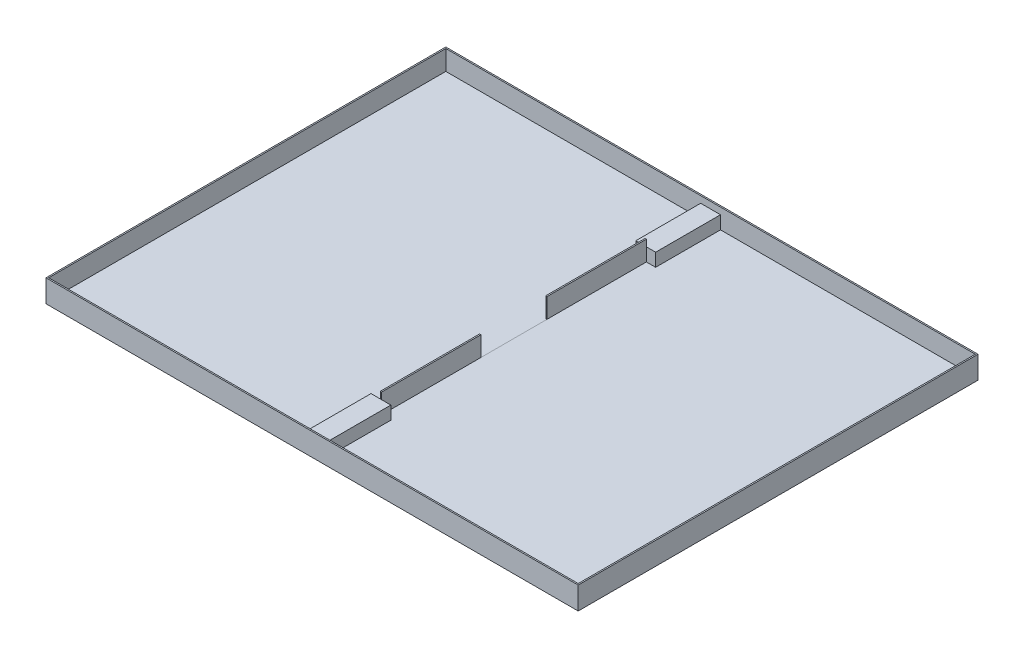
SolidWorks part; units mm, degrees
material "Balsa"
ref_plane "Plano frontal" through (0, 0, 0) normal (0, 0, 1) x (1, 0, 0)
ref_plane "Plano superior" through (0, 0, 0) normal (0, 1, 0) x (1, 0, 0)
ref_plane "Plano direito" through (0, 0, 0) normal (1, 0, 0) x (0, 0, -1)
sketch "Esboço1" plane through (0, 0, 0) normal (0, 0, 1) x (1, 0, 0)
  line L0 (3179.7534, -132.1233) -> (-840.2466, -132.1233)
  line L1 (-840.2466, -132.1233) -> (-840.2466, -152.1233)
  line L4 (-840.2466, -152.1233) -> (3179.7534, -152.1233)
  line L5 (3179.7534, -152.1233) -> (3179.7534, -132.1233)
  dimension "D1" = 4020
  dimension "D3" = 20
extrude "Ressalto-extrusão1" add sketch "Esboço1" along normal blind 3020
sketch "Esboço2" plane through (0, -132.1233, 0) normal (0, 1, 0) x (1, 0, 0)
  line L0 (-830.2466, -10) -> (-830.2466, -3010)
  line L1 (-840.2466, 0) -> (3179.7534, 0)
  line L2 (-840.2466, 0) -> (-840.2466, -3020)
  line L3 (-840.2466, -3020) -> (3179.7534, -3020)
  line L4 (3179.7534, 0) -> (3179.7534, -3020)
  line L5 (-830.2466, -3010) -> (3169.7534, -3010)
  line L6 (3169.7534, -10) -> (3169.7534, -3010)
  line L7 (-830.2466, -10) -> (3169.7534, -10)
  line L8 (1169.7534, -500) -> (1169.7534, -1250) construction
  line L9 (1164.7534, -500) -> (1164.7534, -1250)
  line L10 (1174.7534, -500) -> (1174.7534, -1250)
  line L11 (976.4547, -1500) -> (1352.409, -1500) construction
  line L12 (1164.7534, -1750) -> (1174.7534, -1750)
  line L13 (1164.7534, -1250) -> (1174.7534, -1250)
  line L14 (1164.7534, -2500) -> (1174.7534, -2500)
  line L15 (1164.7534, -1750) -> (1164.7534, -2500)
  line L16 (1164.7534, -10) -> (1164.7534, -2990) construction
  line L17 (1169.7534, -1750) -> (1169.7534, -2500) construction
  line L18 (1169.7534, -10) -> (1169.7534, -2990) construction
  line L19 (1174.7534, -1750) -> (1174.7534, -2500)
  line L20 (1174.7534, -10) -> (1174.7534, -2990) construction
  line L21 (1164.7534, -500) -> (1174.7534, -500)
  line L23 (-830.2466, -10) -> (3169.7534, -10) construction
  line L25 (-830.2466, -3010) -> (3169.7534, -3010) construction
  line L26 (976.4547, -500) -> (1352.409, -500) construction
  line L27 (976.4547, -2500) -> (1352.409, -2500) construction
  point P37 (1169.7534, -10)
  line M9 (3179.7534, 0) -> (-840.2466, 0)
  line M10 (-840.2466, 0) -> (-840.2466, -3020)
  line M11 (-840.2466, -3020) -> (3179.7534, -3020)
  line M12 (3179.7534, -3020) -> (3179.7534, 0)
  dimension "D4" = 500
  dimension "D1" = 10
  dimension "D2" = 5
  dimension "D3" = 5
  dimension "D5" = 1000
  dimension "D6" = 1000
extrude "Ressalto-extrusão2" add sketch "Esboço2" along normal blind 150 contours L19 L12 L15 L14 | L21 L9 L13 L10 | L0 L7 L6 L5 M12 M9 M10 M11
sketch "Esboço3" plane through (0, -132.1233, 0) normal (0, 1, 0) x (1, 0, 0)
  line L0 (1169.7534, -500) -> (1169.7534, -10) construction
  line L1 (1164.7534, -500) -> (1174.7534, -500) construction
  line L2 (-830.2466, -10) -> (3169.7534, -10) construction
  line L3 (1169.7534, -2500) -> (1169.7534, -3010) construction
  line L4 (1094.7534, -10) -> (1244.7534, -10)
  line L5 (1094.7534, -10) -> (1094.7534, -500)
  line L6 (1094.7534, -500) -> (1244.7534, -500)
  line L7 (1244.7534, -10) -> (1244.7534, -500)
  line L8 (1094.7534, -10) -> (1244.7534, -500) construction
  line L9 (1094.7534, -500) -> (1244.7534, -10) construction
  line L10 (1164.7534, -2500) -> (1174.7534, -2500) construction
  line L11 (-830.2466, -3010) -> (3169.7534, -3010) construction
  line L13 (1094.7534, -2500) -> (1244.7534, -2500)
  line L14 (1094.7534, -2500) -> (1094.7534, -3010)
  line L15 (1094.7534, -3010) -> (1244.7534, -3010)
  line L16 (1244.7534, -2500) -> (1244.7534, -3010)
  line L17 (1094.7534, -2500) -> (1244.7534, -3010) construction
  line L18 (1094.7534, -3010) -> (1244.7534, -2500) construction
  point P6 (1169.7534, -255)
  point P11 (1169.7534, -2755)
  dimension "D1" = 150
extrude "Ressalto-extrusão3" add sketch "Esboço3" along normal blind 100
sketch "Esboço4" plane through (0, -132.1233, 0) normal (0, 1, 0) x (1, 0, 0)
  line L0 (1174.7534, -1750) -> (1174.7534, -2500) construction
  line L1 (3169.7534, -10) -> (1174.7534, -10)
  line L2 (3169.7534, -10) -> (3169.7534, -3010)
  line L3 (3169.7534, -3010) -> (1174.7534, -3010)
  line L4 (1174.7534, -10) -> (1174.7534, -3010)
  line L5 (-830.2466, -3010) -> (1094.7534, -3010) construction
extrude "Ressalto-extrusão4" add sketch "Esboço4" along normal blind 1
